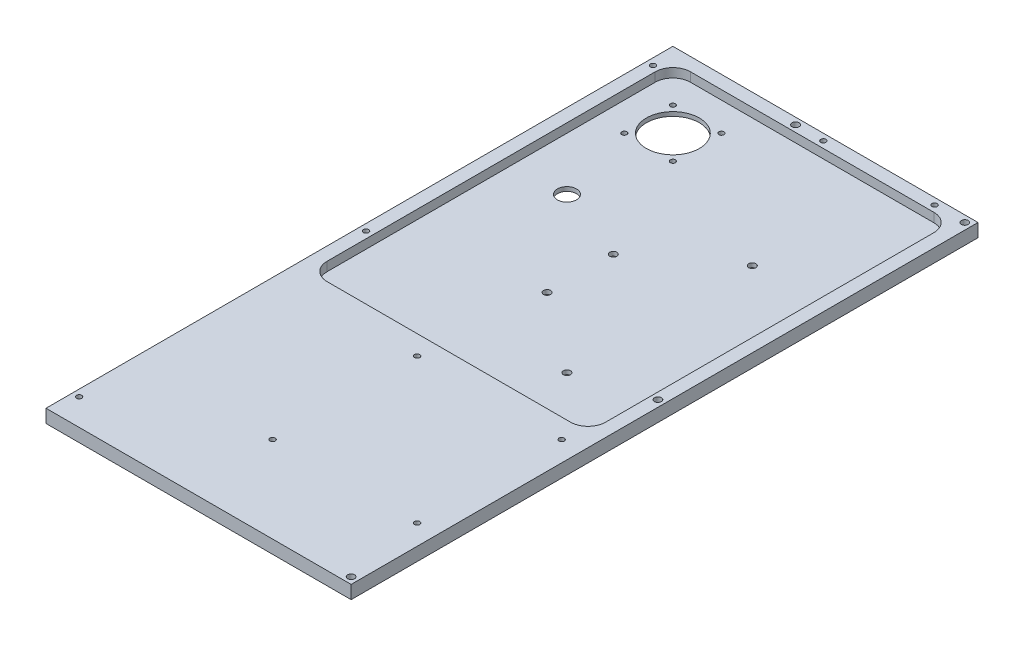
SolidWorks part; units mm, degrees
material "6061-T6 (SS)"
ref_plane "Front Plane" through (0, 0, 0) normal (0, 0, 1) x (1, 0, 0)
ref_plane "Top Plane" through (0, 0, 0) normal (0, 1, 0) x (1, 0, 0)
ref_plane "Right Plane" through (0, 0, 0) normal (1, 0, 0) x (0, 0, -1)
sketch "Sketch1" plane through (0, 0, 0) normal (0, 1, 0) x (1, 0, 0)
  line L0 (-109.7625, 225.5) -> (109.7625, -225.5) construction
  line L1 (-109.7625, 225.5) -> (109.7625, 225.5)
  line L2 (-109.7625, 225.5) -> (-109.7625, -225.5)
  line L3 (-109.7625, -225.5) -> (109.7625, -225.5)
  line L4 (109.7625, 225.5) -> (109.7625, -225.5)
  point P4 (0, 0)
  dimension "D1" = 451
  dimension "D2" = 219.525
extrude "Boss-Extrude1" add sketch "Sketch1" along normal blind 9.525
sketch "Sketch2" plane through (0, 9.525, 0) normal (0, 1, 0) x (1, 0, 0)
  line L0 (43.2625, -111.5) -> (43.2625, -280.9443) construction
  line L7 (100.2375, -45.5) -> (-100.2375, -45.5)
  line L8 (-100.2375, 215.975) -> (-100.2375, -215.975)
  line L9 (-100.2375, -215.975) -> (100.2375, -215.975)
  line L10 (100.2375, -215.975) -> (100.2375, 215.975)
  line L11 (100.2375, 215.975) -> (-100.2375, 215.975)
  line L12 (-100.2375, 215.975) -> (-100.2375, -45.5)
  line L14 (100.2375, -45.5) -> (100.2375, 215.975)
  line L15 (100.2375, 215.975) -> (-100.2375, 215.975)
  line L21 (30.7625, -225.5) -> (30.7625, -540.6284) construction
  line L23 (-109.7625, -111.5) -> (266.5389, -111.5) construction
  line L24 (-109.7625, 225.5) -> (-109.7625, -225.5) construction
  line L26 (-109.7625, -225.5) -> (109.7625, -225.5) construction
  line L27 (109.7625, -225.5) -> (109.7625, 225.5) construction
  dimension "D2" = 12.5
  dimension "D7" = 79
  dimension "D8" = 180
  dimension "D10" = 114
  dimension "D1" = 9.525
extrude "Cut-Extrude1" cut sketch "Sketch2" against normal offset from surface (6.525 mm away) 3 up to face at (0, 0, 0)
fillet "Fillet1" radius 12.7 4 edges at (-100.2375, 6.2625, -215.975) (100.2375, 6.2625, -215.975) (100.2375, 6.2625, 45.5) (-100.2375, 6.2625, 45.5)
hole_wizard "#10-24 Tapped Hole3" positions "Sketch6" profile "Sketch5" tap size "#10-24" standard "ANSI Inch" end condition through all
sketch "Sketch6" plane through (0, 9.525, 0) normal (0, 1, 0) x (1, 0, 0)
  line L2 (43.2625, -111.5) -> (43.2625, -191.2981) construction
  line L4 (-8.7375, -59.5) -> (95.2625, -59.5)
  line L5 (-8.7375, -59.5) -> (-8.7375, -163.5)
  line L6 (-8.7375, -163.5) -> (95.2625, -163.5)
  line L7 (95.2625, -59.5) -> (95.2625, -163.5)
  line L8 (-8.7375, -59.5) -> (95.2625, -163.5) construction
  line L9 (-8.7375, -163.5) -> (95.2625, -59.5) construction
  point P0 (-8.7375, -59.5)
  point P10 (95.2625, -59.5)
  point P106 (-8.7375, -163.5)
  point P108 (95.2625, -163.5)
  dimension "D1" = 104
sketch "Sketch5" plane through (-8.7375, 9.525, 59.5) normal (1, 0, 0) x (0, 0, 1)
  line L0 (0, 0) -> (0, 9.525)
  line L1 (0, 9.525) -> (1.8986, 9.525)
  line L2 (1.8986, 9.525) -> (1.8986, 0)
  line L5 (1.8986, 0) -> (0, 0)
  line L11 (0, -6.35) -> (0, 107.95) construction
  dimension "Thread Major Dia." = 3.7973
  dimension "Thru Tap Drill Depth" = 9.525
hole_wizard "#10-24 Tapped Hole1" positions "Sketch8" profile "Sketch7" tap size "#10-24" standard "ANSI Inch" end condition through all
sketch "Sketch8" plane through (0, 9.525, 0) normal (0, 1, 0) x (1, 0, 0)
  line L0 (87.5375, 215.975) -> (-87.5375, 215.975) construction
  line L1 (109.7625, 225.5) -> (-109.7625, 225.5) construction
  line L2 (95.2625, -59.5) -> (95.2625, -112.8672) construction
  line L3 (-8.7375, -59.5) -> (-8.7375, -101.1208) construction
  line L4 (83.2625, 220.7375) -> (3.2625, 220.7375) construction
  line L5 (-8.7375, -59.5) -> (95.2625, -59.5) construction
  line L7 (43.2625, -59.5) -> (43.2625, -17.8598) construction
  circle A0 centre (83.2625, 220.7375) radius 4.7625 construction
  point P0 (83.2625, 220.7375)
  point P20 (3.2625, 220.7375)
  point P33 (43.2625, 220.7375)
  dimension "D1" = 80
sketch "Sketch7" plane through (83.2625, 9.525, -220.7375) normal (1, 0, 0) x (0, 0, 1)
  line L0 (0, 0) -> (0, 9.525)
  line L1 (0, 9.525) -> (1.8986, 9.525)
  line L2 (1.8986, 9.525) -> (1.8986, 0)
  line L5 (1.8986, 0) -> (0, 0)
  line L11 (0, -6.35) -> (0, 107.95) construction
  dimension "Thread Major Dia." = 3.7973
  dimension "Thru Tap Drill Depth" = 9.525
sketch "Sketch9" plane through (0, 3, 0) normal (0, 1, 0) x (1, 0, 0)
  line L0 (-87.5375, 215.975) -> (87.5375, 215.975) construction
  line L2 (-100.2375, -32.8) -> (-100.2375, 203.275) construction
  circle A0 centre (-62.1375, 177.875) radius 38.1 construction
  circle A1 centre (-62.1375, 177.875) radius 19.05
  dimension "D1" = 76.2
  dimension "D2" = 38.1
extrude "Cut-Extrude2" cut sketch "Sketch9" against normal through all
hole_wizard "#6 Clearance Hole1" positions "Sketch11" profile "Sketch10" hole size "#6" standard "ANSI Inch"
sketch "Sketch11" plane through (0, 3, 0) normal (0, 1, 0) x (1, 0, 0)
  line L1 (-79.6, 195.3375) -> (-44.675, 195.3375) construction
  line L2 (-79.6, 195.3375) -> (-79.6, 160.4125) construction
  line L3 (-79.6, 160.4125) -> (-44.675, 160.4125) construction
  line L4 (-44.675, 195.3375) -> (-44.675, 160.4125) construction
  line L5 (-79.6, 195.3375) -> (-44.675, 160.4125) construction
  line L6 (-79.6, 160.4125) -> (-44.675, 195.3375) construction
  point P0 (-44.675, 195.3375)
  point P3 (-62.1375, 177.875)
  point P187 (-44.675, 160.4125)
  point P189 (-79.6, 160.4125)
  point P191 (-79.6, 195.3375)
  dimension "D1" = 34.925
sketch "Sketch10" plane through (-44.675, 3, -195.3375) normal (1, 0, 0) x (0, 0, 1)
  line L0 (0, 0) -> (0, 4.0989)
  line L1 (0, 4.0989) -> (1.8288, 3)
  line L2 (1.8288, 3) -> (1.8288, 0)
  line L5 (1.8288, 0) -> (0, 0)
  line L10 (0, 4.0989) -> (-1.8288, 3) construction
  line L11 (0, -6.35) -> (0, 107.95) construction
  dimension "Hole Dia." = 3.6576
  dimension "Hole Depth" = 3
  dimension "Drill Angle" = 118
sketch "Sketch12" plane through (0, 3, 0) normal (0, 1, 0) x (1, 0, 0)
  line L0 (-62.1375, 177.875) -> (-62.1375, 101.675) construction
  circle A0 centre (-62.1375, 101.675) radius 6.858
  dimension "D1" = 13.716
  dimension "D2" = 76.2
extrude "Cut-Extrude3" cut sketch "Sketch12" against normal through all
hole_wizard "#10 Clearance Hole1" positions "Sketch14" profile "Sketch13" hole size "#10" standard "ANSI Inch" end condition through all
sketch "Sketch14" plane through (0, 9.525, 0) normal (0, 1, 0) x (1, 0, 0)
  line L0 (109.7625, -225.5) -> (109.7625, 225.5) construction
  line L1 (109.7625, 225.5) -> (-109.7625, 225.5) construction
  line L3 (100.2375, 203.275) -> (100.2375, -32.8) construction
  line L4 (109.7625, 0) -> (136.8478, 0) construction
  line L5 (105, 220.7375) -> (105, 151.9831) construction
  circle A0 centre (105, 220.7375) radius 4.7625 construction
  point P0 (105, 220.7375)
  point P20 (105, 0)
  point P24 (105, -220.7375)
sketch "Sketch13" plane through (105, 9.525, -220.7375) normal (1, 0, 0) x (0, 0, 1)
  line L0 (0, 0) -> (0, 9.525)
  line L1 (0, 9.525) -> (2.4892, 9.525)
  line L2 (2.4892, 9.525) -> (2.4892, 0)
  line L5 (2.4892, 0) -> (0, 0)
  line L11 (0, -6.35) -> (0, 107.95) construction
  dimension "Thru Hole Dia." = 4.9784
  dimension "Thru Hole Depth" = 9.525
hole_wizard "#10-24 Tapped Hole4" positions "Sketch16" profile "Sketch15" tap size "#10-24" standard "ANSI Inch"
sketch "Sketch16" plane through (0, 9.525, 0) normal (0, 1, 0) x (1, 0, 0)
  line L0 (-100.2375, 203.275) -> (-100.2375, -32.8) construction
  line L1 (-109.7625, 225.5) -> (-109.7625, -225.5) construction
  line L2 (109.7625, 225.5) -> (-109.7625, 225.5) construction
  line L3 (0, 0) -> (-47.2753, 0) construction
  line L4 (-105, 176.9096) -> (-105, 143.6046) construction
  circle A0 centre (-105, 206.45) radius 4.7625 construction
  point P0 (-105, 206.45)
  point P17 (-105, 0)
  point P22 (-105, -206.45)
  dimension "D1" = 19.05
sketch "Sketch15" plane through (-105, 9.525, -206.45) normal (1, 0, 0) x (0, 0, 1)
  line L0 (0, 0) -> (0, 19.1708)
  line L1 (0, 19.1708) -> (1.8986, 18.03)
  line L2 (1.8986, 18.03) -> (1.8986, 0)
  line L5 (1.8986, 0) -> (0, 0)
  line L10 (0, 19.1708) -> (-1.8986, 18.03) construction
  line L11 (0, -6.35) -> (0, 107.95) construction
  dimension "Tap Drill Dia." = 3.7973
  dimension "Tap Drill Depth" = 18.03
  dimension "Drill Angle" = 118
cosmetic thread "Hole Thread3" parameters "D1"=9.525, "D2"=4.826
cosmetic thread "Hole Thread4" parameters "D1"=9.525, "D2"=4.826
cosmetic thread "Hole Thread5" parameters "D1"=9.525, "D2"=4.826
hole_wizard "#10 Clearance Hole2" positions "Sketch18" profile "Sketch17" hole size "#10" standard "ANSI Inch"
sketch "Sketch18" plane through (0, 3, 0) normal (0, 1, 0) x (1, 0, 0)
  line L1 (-109.7625, 225.5) -> (-109.7625, -225.5) construction
  line L2 (-8.1625, 81.0375) -> (-8.1625, 33.4125) construction
  line L3 (-8.1625, 57.225) -> (48.9875, 57.225) construction
  line L4 (48.9875, 123.9) -> (48.9875, -9.45) construction
  line L5 (109.7625, 225.5) -> (-109.7625, 225.5) construction
  point P0 (-8.1625, 81.0375)
  point P2 (-8.1625, 33.4125)
  point P4 (48.9875, 123.9)
  point P6 (48.9875, -9.45)
  point P23 (48.9875, 57.225)
  dimension "D1" = 101.6
  dimension "D2" = 101.6
  dimension "D3" = 47.625
  dimension "D4" = 57.15
  dimension "D5" = 133.35
sketch "Sketch17" plane through (-8.1625, 3, -81.0375) normal (1, 0, 0) x (0, 0, 1)
  line L0 (0, 0) -> (0, 137.4238)
  line L1 (0, 137.4238) -> (2.5527, 135.89)
  line L2 (2.5527, 135.89) -> (2.5527, 0)
  line L5 (2.5527, 0) -> (0, 0)
  line L10 (0, 137.4238) -> (-2.5527, 135.89) construction
  line L11 (0, -6.35) -> (0, 107.95) construction
  dimension "Hole Dia." = 5.1054
  dimension "Hole Depth" = 135.89
  dimension "Drill Angle" = 118
hole_wizard "1/4-20 Tapped Hole1" positions "Sketch20" profile "Sketch19" tap size "1/4-20" standard "ANSI Inch"
sketch "Sketch20" plane through (0, 9.525, 0) normal (0, 1, 0) x (1, 0, 0)
  line L0 (3.2625, 220.7375) -> (-16.7375, 220.7375)
  point P0 (-16.7375, 220.7375)
  dimension "D1" = 20
sketch "Sketch19" plane through (-16.7375, 9.525, -220.7375) normal (1, 0, 0) x (0, 0, 1)
  line L0 (0, 0) -> (0, 18.6838)
  line L1 (0, 18.6838) -> (2.5527, 17.15)
  line L2 (2.5527, 17.15) -> (2.5527, 0)
  line L5 (2.5527, 0) -> (0, 0)
  line L10 (0, 18.6838) -> (-2.5527, 17.15) construction
  line L11 (0, -6.35) -> (0, 107.95) construction
  dimension "Tap Drill Dia." = 5.1054
  dimension "Tap Drill Depth" = 17.15
  dimension "Drill Angle" = 118
cosmetic thread "Hole Thread6" parameters "D1"=7.62, "D2"=6.35
